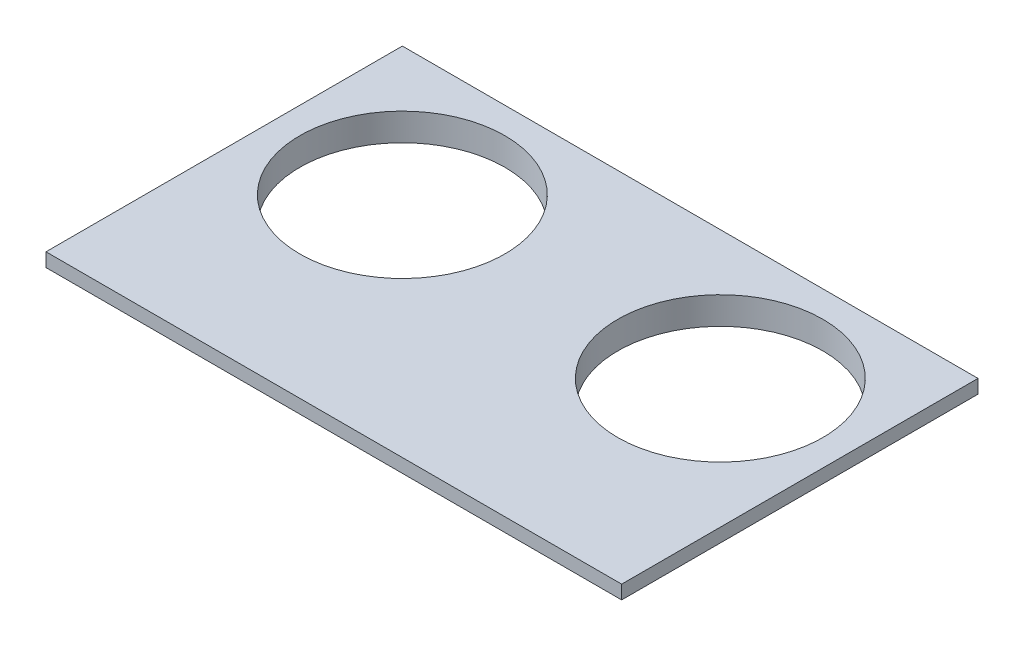
SolidWorks part; units mm, degrees
ref_plane "Front Plane" through (0, 0, 0) normal (0, 0, 1) x (1, 0, 0)
ref_plane "Top Plane" through (0, 0, 0) normal (0, 1, 0) x (1, 0, 0)
ref_plane "Right Plane" through (0, 0, 0) normal (1, 0, 0) x (0, 0, -1)
sketch "Sketch1" plane through (0, 0, 0) normal (0, 1, 0) x (1, 0, 0)
  line L1 (-52.5, -32.5) -> (52.5, -32.5)
  line L2 (-52.5, -32.5) -> (-52.5, 32.5)
  line L3 (-52.5, 32.5) -> (52.5, 32.5)
  line L4 (52.5, -32.5) -> (52.5, 32.5)
  line L5 (-52.5, -32.5) -> (52.5, 32.5) construction
  line L6 (-52.5, 32.5) -> (52.5, -32.5) construction
  point P0 (0, 0)
  dimension "D1" = 105
  dimension "D2" = 65
extrude "Boss-Extrude1" add sketch "Sketch1" along normal blind 5
sketch "Sketch2" plane through (0, 0, 0) normal (0, -1, 0) x (1, 0, 0)
  line L0 (-52.5, 32.5) -> (52.5, 32.5) construction
  line L1 (-50, -30) -> (50, -30)
  line L2 (-50, -30) -> (-50, 30)
  line L3 (-50, 30) -> (50, 30)
  line L4 (50, -30) -> (50, 30)
  line L5 (-50, -30) -> (50, 30) construction
  line L6 (-50, 30) -> (50, -30) construction
  line L7 (-52.5, -32.5) -> (-52.5, 32.5) construction
  line L9 (-52.5, -32.5) -> (52.5, -32.5)
  line L10 (-52.5, -32.5) -> (-52.5, 32.5)
  line L11 (-52.5, 32.5) -> (52.5, 32.5)
  line L12 (52.5, -32.5) -> (52.5, 32.5)
  line L13 (-52.5, -32.5) -> (52.5, 32.5) construction
  line L14 (-52.5, 32.5) -> (52.5, -32.5) construction
  point P0 (0, 0)
  point P10 (0, 0)
  dimension "D1" = 2.5
  dimension "D2" = 2.5
extrude "Cut-Extrude1" cut sketch "Sketch2" against normal blind 2.5
sketch "Sketch3" plane through (0, 5, 0) normal (0, 1, 0) x (1, 0, 0)
  line L0 (52.5, 32.5) -> (-52.5, 32.5) construction
  line L1 (-52.5, 32.5) -> (-52.5, -32.5) construction
  line L2 (52.5, -32.5) -> (52.5, 32.5) construction
  circle A0 centre (-29, 9) radius 18.7
  circle A1 centre (29, 9) radius 18.7
  point P10 (0, 0)
  dimension "D1" = 23.5
  dimension "D2" = 23.5
  dimension "D3" = 23.5
  dimension "D4" = 23.5
extrude "Cut-Extrude2" cut sketch "Sketch3" against normal blind 50
